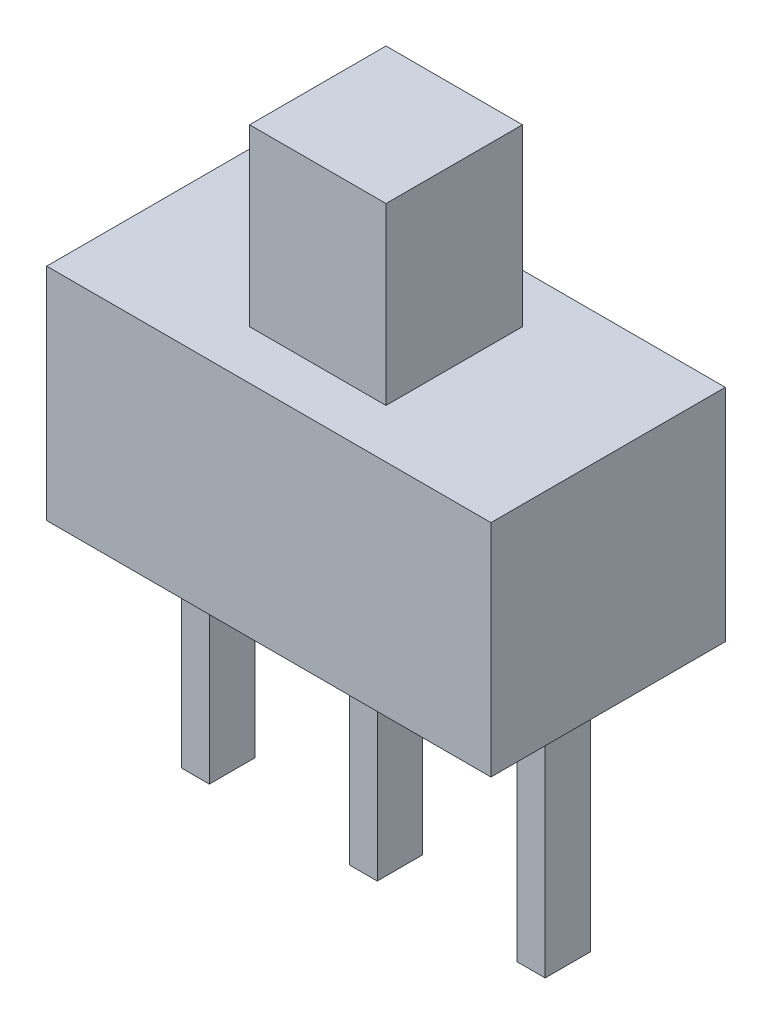
SolidWorks part; units mm, degrees
ref_plane "前视基准面" through (0, 0, 0) normal (0, 0, 1) x (1, 0, 0)
ref_plane "上视基准面" through (0, 0, 0) normal (0, 1, 0) x (1, 0, 0)
ref_plane "右视基准面" through (0, 0, 0) normal (1, 0, 0) x (0, 0, -1)
sketch "草图1" plane through (0, 0, 0) normal (0, 1, 0) x (1, 0, 0)
  line L1 (-6.35, 3.35) -> (6.35, 3.35)
  line L2 (-6.35, 3.35) -> (-6.35, -3.35)
  line L3 (-6.35, -3.35) -> (6.35, -3.35)
  line L4 (6.35, 3.35) -> (6.35, -3.35)
  line L5 (-6.35, 3.35) -> (6.35, -3.35) construction
  line L6 (-6.35, -3.35) -> (6.35, 3.35) construction
  point P0 (0, 0)
  dimension "D1" = 12.7
  dimension "D2" = 6.7
extrude "凸台-拉伸1" add sketch "草图1" along normal blind 6.3
sketch "草图2" plane through (0, 6.3, 0) normal (0, 1, 0) x (1, 0, 0)
  line L1 (-1.95, -1.95) -> (1.95, -1.95)
  line L2 (-1.95, -1.95) -> (-1.95, 1.95)
  line L3 (-1.95, 1.95) -> (1.95, 1.95)
  line L4 (1.95, -1.95) -> (1.95, 1.95)
  line L5 (-1.95, -1.95) -> (1.95, 1.95) construction
  line L6 (-1.95, 1.95) -> (1.95, -1.95) construction
  point P0 (0, 0)
  dimension "D1" = 3.9
  dimension "D2" = 3.9
extrude "凸台-拉伸2" add sketch "草图2" along normal blind 5
sketch "草图3" plane through (0, 0, 0) normal (0, -1, 0) x (1, 0, 0)
  line L0 (-0.4, -0.65) -> (0.4, -0.65)
  line L5 (-0.4, -0.65) -> (-0.4, 0.65)
  line L6 (-0.4, 0.65) -> (0.4, 0.65)
  line L11 (0.4, -0.65) -> (0.4, 0.65)
  line L12 (-0.4, -0.65) -> (0.4, 0.65) construction
  line L13 (4.4, -0.65) -> (5.2, -0.65)
  line L14 (4.4, -0.65) -> (4.4, 0.65)
  line L15 (4.4, 0.65) -> (5.2, 0.65)
  line L16 (5.2, -0.65) -> (5.2, 0.65)
  line L17 (4.4, -0.65) -> (5.2, 0.65) construction
  line L18 (4.4, 0.65) -> (5.2, -0.65) construction
  line L19 (-0.4, 0.65) -> (0.4, -0.65) construction
  line L20 (-5.2, -0.65) -> (-4.4, -0.65)
  line L21 (-5.2, -0.65) -> (-5.2, 0.65)
  line L22 (-5.2, 0.65) -> (-4.4, 0.65)
  line L23 (-4.4, -0.65) -> (-4.4, 0.65)
  line L24 (-5.2, -0.65) -> (-4.4, 0.65) construction
  line L25 (-5.2, 0.65) -> (-4.4, -0.65) construction
  point P0 (0, 0)
  point P5 (-4.8, 0)
  point P10 (0, 0)
  point P11 (4.8, 0)
  point P17 (0, 0)
  dimension "D1" = 1.3
  dimension "D2" = 0.8
  dimension "D3" = 1.3
  dimension "D4" = 0.8
  dimension "D5" = 1.3
  dimension "D6" = 0.8
  dimension "D7" = 4.8
  dimension "D8" = 4.8
extrude "凸台-拉伸3" add sketch "草图3" along normal blind 6.9
